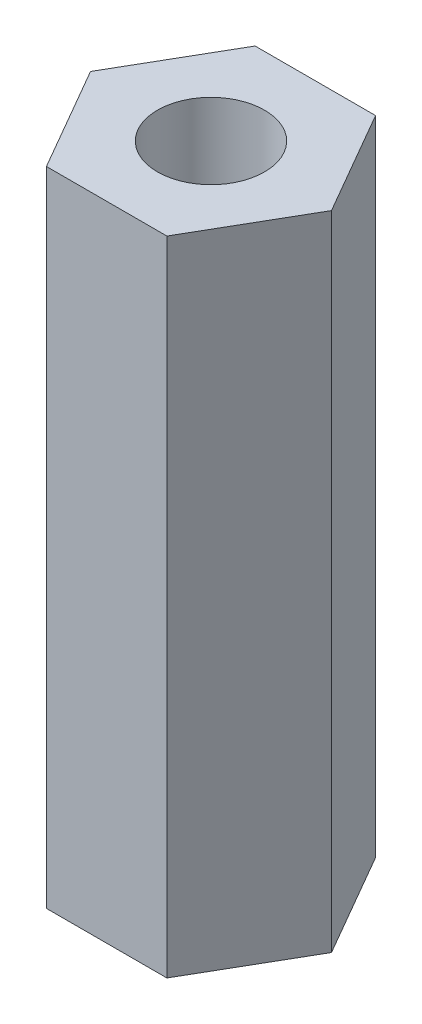
SolidWorks part; units mm, degrees
ref_plane "Front Plane" through (0, 0, 0) normal (0, 0, 1) x (1, 0, 0)
ref_plane "Top Plane" through (0, 0, 0) normal (0, 1, 0) x (1, 0, 0)
ref_plane "Right Plane" through (0, 0, 0) normal (1, 0, 0) x (0, 0, -1)
sketch "Sketch1" plane through (0, 0, 0) normal (0, 1, 0) x (1, 0, 0)
  line L1 (2.25, 0) -> (1.125, 1.9486)
  line L2 (1.125, 1.9486) -> (-1.125, 1.9486)
  line L3 (-1.125, 1.9486) -> (-2.25, 0)
  line L4 (-2.25, 0) -> (-1.125, -1.9486)
  line L5 (-1.125, -1.9486) -> (1.125, -1.9486)
  line L6 (1.125, -1.9486) -> (2.25, 0)
  circle A0 centre (0, 0) radius 1.9486 construction
  circle A1 centre (0, 0) radius 1
  dimension "D2" = 2
  dimension "D1" = 4.5
extrude "Boss-Extrude1" add sketch "Sketch1" along normal blind 12
